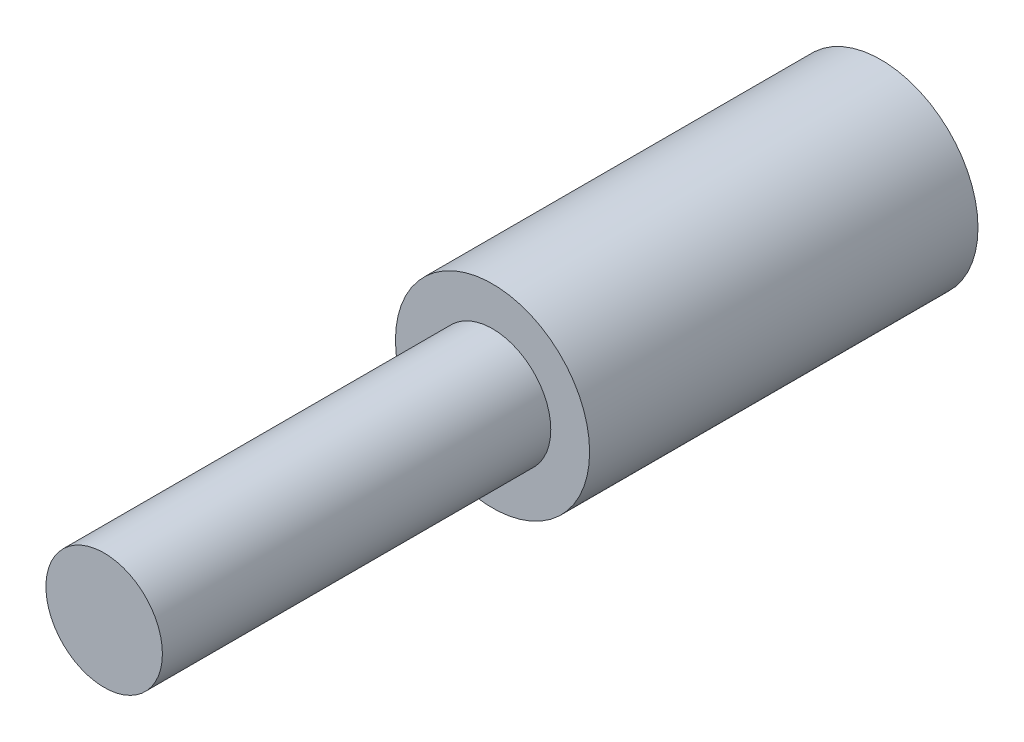
SolidWorks part; units mm, degrees
material "Edelstahl Standard"
ref_plane "Draufsicht" through (0, 0, 0) normal (0, 0, 1) x (1, 0, 0)
ref_plane "Vorderansicht" through (0, 0, 0) normal (0, 1, 0) x (1, 0, 0)
ref_plane "Seitenansicht" through (0, 0, 0) normal (1, 0, 0) x (0, 0, -1)
sketch "Skizze1" plane through (0, 0, 0) normal (0, 0, 1) x (1, 0, 0)
  circle A0 centre (0, 0) radius 25
  dimension "D1-D1" = 50
extrude "Aufsatz-Linear austragen1" add sketch "Skizze1" along normal blind 100
sketch "Skizze2" plane through (0, 0, 100) normal (0, 0, 1) x (1, 0, 0)
  circle A0 centre (0, 0) radius 15
  circle A2 centre (0, 0) radius 25 construction
  dimension "D1" = 10
extrude "Aufsatz-Linear austragen2" add sketch "Skizze2" along normal blind 100
